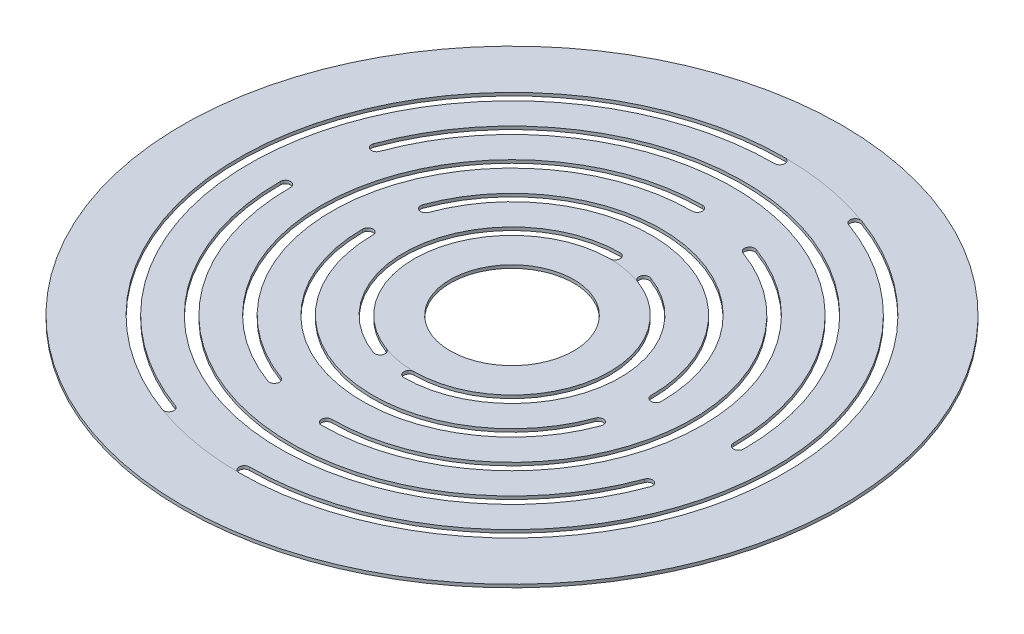
SolidWorks part; units mm, degrees
ref_plane "Front Plane" through (0, 0, 0) normal (0, 0, 1) x (1, 0, 0)
ref_plane "Top Plane" through (0, 0, 0) normal (0, 1, 0) x (1, 0, 0)
ref_plane "Right Plane" through (0, 0, 0) normal (1, 0, 0) x (0, 0, -1)
sketch "Sketch1" plane through (0, 0, 0) normal (0, 1, 0) x (1, 0, 0)
  line L0 (0, 32) -> (0, -32) construction
  line L1 (-32, 0) -> (32, 0) construction
  line L2 (-10.9446, -30.0702) -> (10.9446, 30.0702) construction
  line L3 (30.0702, -10.9446) -> (-30.0702, 10.9446) construction
  circle A0 centre (0, 0) radius 32
  circle A1 centre (0, 0) radius 6
  arc A2 (0, 10) -> (-3.4202, -9.3969) centre (0, 0) ccw
  arc A3 (-14, 0) -> (13.1557, -4.7883) centre (0, 0) ccw
  arc A4 (0, 18) -> (-6.1564, -16.9145) centre (0, 0) ccw
  arc A5 (-22, 0) -> (20.6732, -7.5244) centre (0, 0) ccw
  arc A6 (0, 26) -> (-8.8925, -24.432) centre (0, 0) ccw
  arc A8 (22, 0) -> (-20.6732, 7.5244) centre (0, 0) ccw
  arc A9 (14, 0) -> (-13.1557, 4.7883) centre (0, 0) ccw
  arc A10 (0, -26) -> (8.8925, 24.432) centre (0, 0) ccw
  arc A11 (0, -18) -> (6.1564, 16.9145) centre (0, 0) ccw
  arc A12 (0, -10) -> (3.4202, 9.3969) centre (0, 0) ccw
  arc A13 (0, 26.5) -> (-9.0635, -24.9019) centre (0, 0) ccw
  arc A14 (22.5, 0) -> (-21.1431, 7.6955) centre (0, 0) ccw
  arc A15 (0, -26.5) -> (9.0635, 24.9019) centre (0, 0) ccw
  arc A16 (0, 18.5) -> (-6.3274, -17.3843) centre (0, 0) ccw
  arc A17 (14.5, 0) -> (-13.6255, 4.9593) centre (0, 0) ccw
  arc A18 (0, -18.5) -> (6.3274, 17.3843) centre (0, 0) ccw
  arc A19 (0, 10.5) -> (-3.5912, -9.8668) centre (0, 0) ccw
  arc A20 (0, -10.5) -> (3.5912, 9.8668) centre (0, 0) ccw
  arc A21 (-14.5, 0) -> (13.6255, -4.9593) centre (0, 0) ccw
  arc A22 (-22.5, 0) -> (21.1431, -7.6955) centre (0, 0) ccw
  arc A23 (0, 25.5) -> (-8.7215, -23.9622) centre (0, 0) ccw
  arc A24 (21.5, 0) -> (-20.2034, 7.3534) centre (0, 0) ccw
  arc A25 (0, -25.5) -> (8.7215, 23.9622) centre (0, 0) ccw
  arc A26 (0, 17.5) -> (-5.9854, -16.4446) centre (0, 0) ccw
  arc A27 (13.5, 0) -> (-12.6859, 4.6173) centre (0, 0) ccw
  arc A28 (0, -17.5) -> (5.9854, 16.4446) centre (0, 0) ccw
  arc A29 (0, 9.5) -> (-3.2492, -8.9271) centre (0, 0) ccw
  arc A30 (0, -9.5) -> (3.2492, 8.9271) centre (0, 0) ccw
  arc A31 (-13.5, 0) -> (12.6859, -4.6173) centre (0, 0) ccw
  arc A32 (-21.5, 0) -> (20.2034, -7.3534) centre (0, 0) ccw
  arc A33 (0, 26.5) -> (0, 25.5) centre (0, 26) cw
  arc A34 (-9.0635, -24.9019) -> (-8.7215, -23.9622) centre (-8.8925, -24.432) ccw
  arc A35 (22.5, 0) -> (21.5, 0) centre (22, 0) cw
  arc A36 (-21.1431, 7.6955) -> (-20.2034, 7.3534) centre (-20.6732, 7.5244) ccw
  arc A37 (0, -26.5) -> (0, -25.5) centre (0, -26) cw
  arc A38 (9.0635, 24.9019) -> (8.7215, 23.9622) centre (8.8925, 24.432) ccw
  arc A39 (0, 18.5) -> (0, 17.5) centre (0, 18) cw
  arc A40 (-6.3274, -17.3843) -> (-5.9854, -16.4446) centre (-6.1564, -16.9145) ccw
  arc A41 (14.5, 0) -> (13.5, 0) centre (14, 0) cw
  arc A42 (-13.6255, 4.9593) -> (-12.6859, 4.6173) centre (-13.1557, 4.7883) ccw
  arc A43 (0, -18.5) -> (0, -17.5) centre (0, -18) cw
  arc A44 (6.3274, 17.3843) -> (5.9854, 16.4446) centre (6.1564, 16.9145) ccw
  arc A45 (0, 10.5) -> (0, 9.5) centre (0, 10) cw
  arc A46 (-3.5912, -9.8668) -> (-3.2492, -8.9271) centre (-3.4202, -9.3969) ccw
  arc A47 (0, -10.5) -> (0, -9.5) centre (0, -10) cw
  arc A48 (3.5912, 9.8668) -> (3.2492, 8.9271) centre (3.4202, 9.3969) ccw
  arc A49 (-14.5, 0) -> (-13.5, 0) centre (-14, 0) cw
  arc A50 (13.6255, -4.9593) -> (12.6859, -4.6173) centre (13.1557, -4.7883) ccw
  arc A51 (-22.5, 0) -> (-21.5, 0) centre (-22, 0) cw
  arc A52 (21.1431, -7.6955) -> (20.2034, -7.3534) centre (20.6732, -7.5244) ccw
  dimension "D1" = 64
  dimension "D2" = 12
  dimension "D3" = 20
  dimension "D4" = 28
  dimension "D5" = 36
  dimension "D6" = 44
  dimension "D7" = 52
  dimension "D8" = 20
  dimension "D9" = 20
  dimension "D10" = 0.5
  dimension "D11" = 0.5
extrude "Boss-Extrude1" add sketch "Sketch1" along normal blind 0.3 contours A0 A52 A22 A51 A32 A50 A21 A49 A31 A48 A20 A47 A30 A46 A19 A45 A29 A44 A18 A43 A28 A42 A17 A41 A27 A40 A16 A39 A26 A38 A15 A37 A25 A36 A14 A35 A24 A34 A13 A33 A23
sketch "Sketch2" plane through (0, 0.3, 0) normal (0, 1, 0) x (1, 0, 0)
  circle A0 centre (0, 0) radius 9.5
  circle A1 centre (0, 0) radius 26.5
split line "Split Line1"
